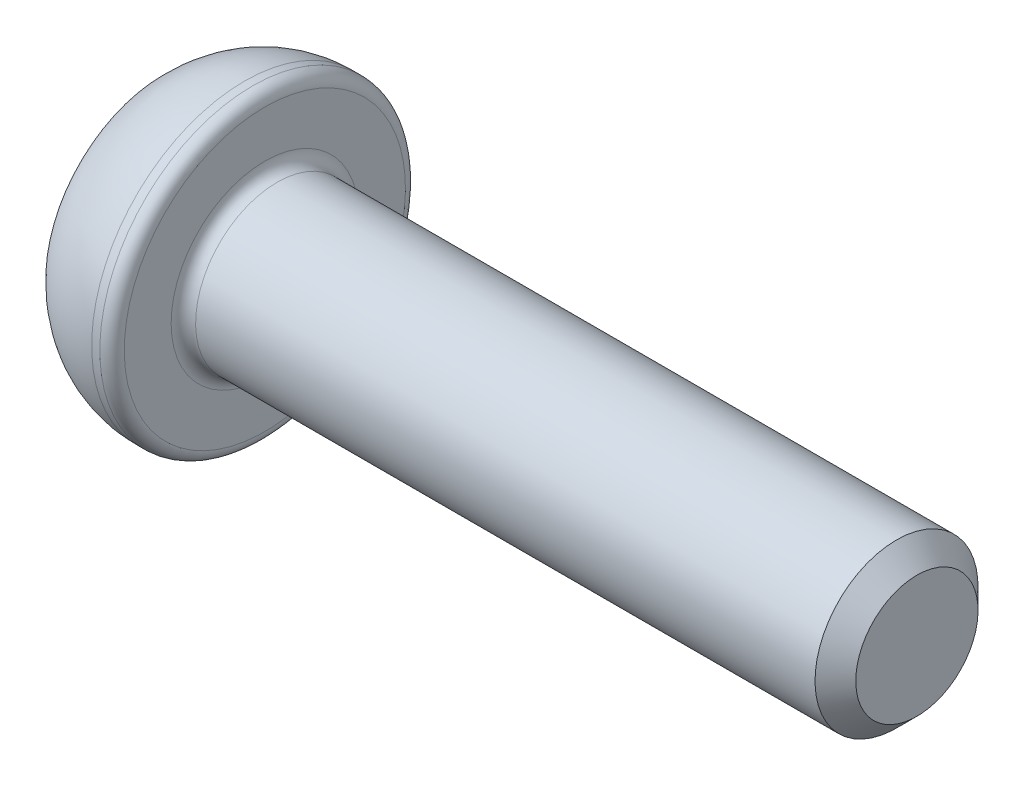
SolidWorks part; units mm, degrees
ref_plane "Спереди" through (0, 0, 0) normal (0, 0, 1) x (1, 0, 0)
ref_plane "Сверху" through (0, 0, 0) normal (0, 1, 0) x (1, 0, 0)
ref_plane "Справа" through (0, 0, 0) normal (1, 0, 0) x (0, 0, -1)
sketch "Эскиз1" plane through (0, 0, 0) normal (0, 0, 1) x (1, 0, 0)
  line L0 (0, 0) -> (0, 2.875)
  line L1 (2, 3.75) -> (2.5, 3.75)
  line L2 (2.5, 3.75) -> (2.5, 2)
  line L3 (2.5, 2) -> (18.5, 2)
  line L4 (18.5, 2) -> (18.5, 0)
  line L5 (18.5, 0) -> (0, 0) construction
  line L6 (0, 0) -> (18.5, 0)
  arc A0 (0, 2.875) -> (2, 3.75) centre (2, 1.0268) cw
  point P9 (2.5, 2.875)
  dimension "D1" = 0.5
  dimension "D2" = 4
  dimension "D3" = 7.5
  dimension "D5" = 2.5
  dimension "D6" = 16
revolve "Повернуть1" add sketch "Эскиз1" angle 360 about L5
cosmetic thread "Условное изображение резьбы1" parameters "D2"=3.22
sketch "Эскиз2" plane through (0, 0, 0) normal (-1, 0, 0) x (0, 0, 1)
  line L1 (0.7217, 1.25) -> (-0.7217, 1.25)
  line L2 (-0.7217, 1.25) -> (-1.4434, 0)
  line L3 (-1.4434, 0) -> (-0.7217, -1.25)
  line L4 (-0.7217, -1.25) -> (0.7217, -1.25)
  line L5 (0.7217, -1.25) -> (1.4434, 0)
  line L6 (1.4434, 0) -> (0.7217, 1.25)
  circle A0 centre (0, 0) radius 1.25 construction
  dimension "D1" = 2.5
extrude "Вырез-Вытянуть1" cut sketch "Эскиз2" against normal blind 1.5
fillet "Скругление1" radius 0.3 2 edges at (2.5, 2, 0) (2.5, 3.75, 0)
chamfer "Фаска1" distance 0.5 angle 45 1 edges at (18.5, 2, 0)
